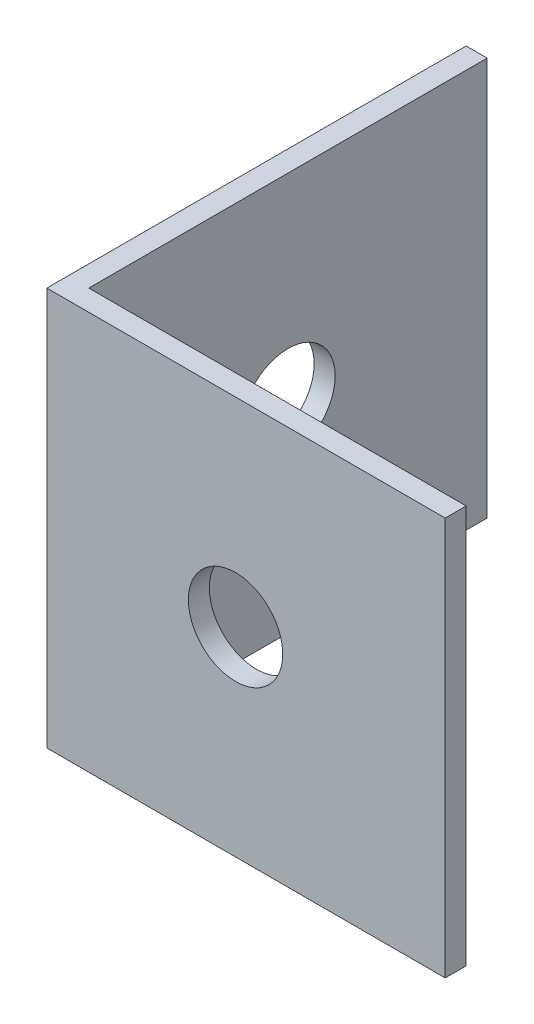
SolidWorks part; units mm, degrees
material "1060 Сплав"
ref_plane "Спереди" through (0, 0, 0) normal (0, 0, 1) x (1, 0, 0)
ref_plane "Сверху" through (0, 0, 0) normal (0, 1, 0) x (1, 0, 0)
ref_plane "Справа" through (0, 0, 0) normal (1, 0, 0) x (0, 0, -1)
sketch "Эскиз1" plane through (0, 0, 0) normal (0, 1, 0) x (1, 0, 0)
  line L0 (0, 0) -> (0, 20)
  line L1 (0, 20) -> (1, 20)
  line L2 (1, 20) -> (1, 1)
  line L3 (1, 1) -> (20, 1)
  line L4 (20, 1) -> (20, 0)
  line L5 (20, 0) -> (0, 0)
  dimension "D1" = 1
  dimension "D2" = 20
extrude "Бобышка-Вытянуть1" add sketch "Эскиз1" along normal blind 19
sketch "Эскиз3" plane through (20, 0, 0) normal (1, 0, 0) x (0, 0, -1)
  line L4 (0, 0) -> (1, 0)
  line L5 (1, 0) -> (1, 19)
  line L6 (1, 19) -> (0, 19)
  line L7 (0, 19) -> (0, 0)
  line L8 (0, 0) -> (1, 0)
  line L9 (1, 0) -> (1, 19)
  line L10 (1, 19) -> (0, 19)
  line L11 (0, 19) -> (0, 0)
  dimension "D1" = 0
extrude "Вырез-Вытянуть1" cut sketch "Эскиз3" against normal blind 1
sketch "Эскиз4" plane through (1, 0, 0) normal (1, 0, 0) x (0, 0, -1)
  line L0 (1, 0) -> (20, 0) construction
  line L3 (20, 19) -> (20, 0) construction
  circle A0 centre (10.5, 9.5) radius 2.25
  dimension "D1" = 4.5
  dimension "D3" = 9.5
  dimension "D2" = 9.5
extrude "Вырез-Вытянуть2" cut sketch "Эскиз4" against normal through all
sketch "Эскиз5" plane through (0, 0, -1) normal (0, 0, -1) x (-1, 0, 0)
  line L1 (-19, 0) -> (-1, 0) construction
  line L4 (-1, 19) -> (-1, 0) construction
  line L5 (-19, 0) -> (-19, 19) construction
  circle A0 centre (-9, 9.5) radius 2.25
  dimension "D1" = 8
  dimension "D2" = 4.5
  dimension "D3" = 9.5
  dimension "D4" = 10
extrude "Вырез-Вытянуть3" cut sketch "Эскиз5" against normal through all
